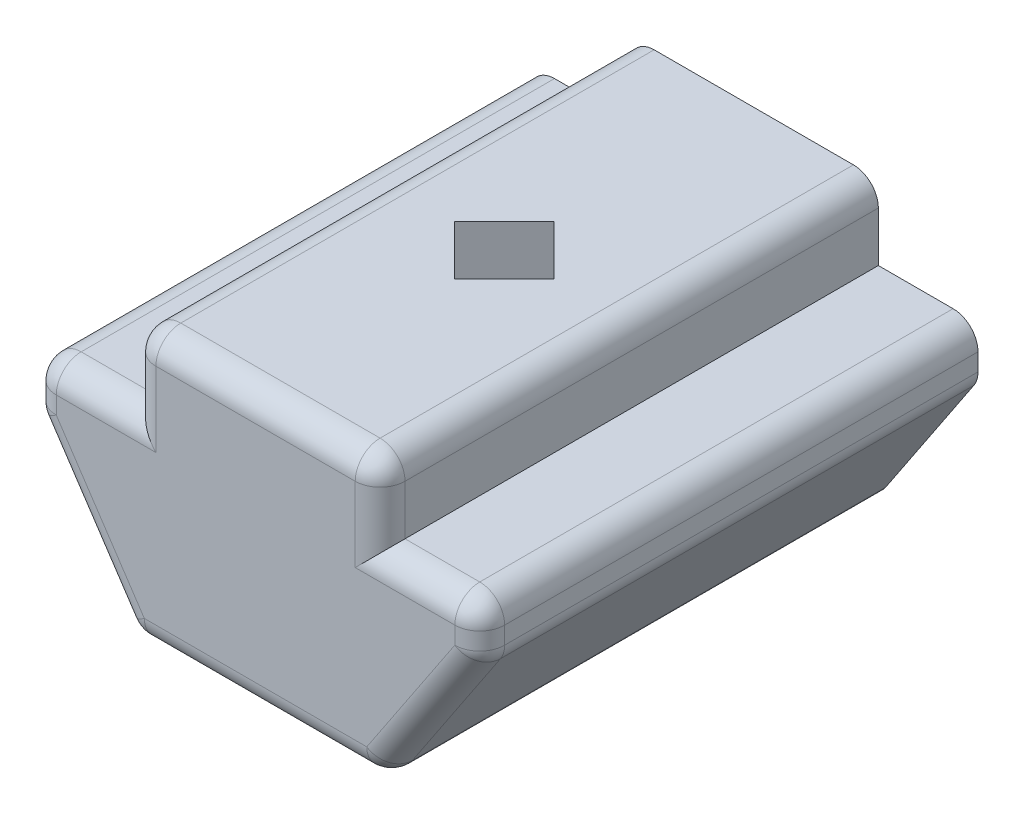
SolidWorks part; units mm, degrees
material "Maple"
ref_plane "Wasteboard" through (0, 0, 0) normal (0, 0, 1) x (1, 0, 0)
ref_plane "Left-Right" through (0, 0, 0) normal (0, 1, 0) x (1, 0, 0)
ref_plane "Front-Back" through (0, 0, 0) normal (1, 0, 0) x (0, 0, -1)
sketch "Sketch1" plane through (0, 0, 0) normal (0, 0, 1) x (1, 0, 0)
  line L10 (-2.5, -4.0476) -> (2.5, -4.0476)
  line L11 (2.5, -4.0476) -> (4.5, -1.0476)
  line L12 (4.5, -1.0476) -> (4.5, -0.0476)
  line L13 (4.5, -0.0476) -> (2.5, -0.0476)
  line L14 (2.5, -0.0476) -> (2.5, 1.4524)
  line L15 (2.5, 1.4524) -> (-2.5, 1.4524)
  line L16 (0, 1.4524) -> (0, 9.7381) construction
  line L17 (-2.5, -0.0476) -> (-2.5, 1.4524)
  line L18 (-4.5, -0.0476) -> (-2.5, -0.0476)
  line L19 (-4.5, -1.0476) -> (-4.5, -0.0476)
  line L20 (-2.5, -4.0476) -> (-4.5, -1.0476)
  point P14 (0, -4.0476)
  dimension "D1" = 5
  dimension "D2" = 5
  dimension "D3" = 3
  dimension "D4" = 1
  dimension "D5" = 1.5
  dimension "D6" = 2
extrude "Boss-Extrude1" add sketch "Sketch1" along normal blind 10
sketch "Sketch4" plane through (0, 1.4524, 0) normal (0, 1, 0) x (1, 0, 0)
  line L1 (-1.0211, -4.9865) -> (-0.0211, -3.9865)
  line L2 (-1.0211, -4.9865) -> (-0.0211, -5.9865)
  line L3 (-0.0211, -5.9865) -> (0.9789, -4.9865)
  line L4 (2.5, 0) -> (-2.5, 0)
  line L5 (-2.5, 0) -> (-2.5, -10)
  line L6 (-2.5, -10) -> (2.5, -10)
  line L7 (2.5, -10) -> (2.5, 0)
  line L8 (2.5, 0) -> (-2.5, 0) construction
  line L9 (-2.5, 0) -> (-2.5, -10) construction
  line L10 (-2.5, -10) -> (2.5, -10) construction
  line L11 (2.5, -10) -> (2.5, 0) construction
  line L12 (-0.0211, -3.9865) -> (0.9789, -4.9865)
  line L13 (-0.7282, -4.2794) -> (0.686, -5.6936) construction
  line L14 (-0.7282, -5.6936) -> (0.686, -4.2794) construction
  circle A0 centre (-0.0211, -4.9865) radius 1 construction
  dimension "D2" = 2
  dimension "D1" = 0
extrude "Cut-Extrude2" cut sketch "Sketch4" against normal through all
fillet "Fillet1" radius 0.5 8 edges at (2.5, -4.0476, 5) (-2.5, -4.0476, 5) (4.5, -1.0476, 5) (4.5, -0.0476, 5) (2.5, 1.4524, 5) (-4.5, -1.0476, 5) (-4.5, -0.0476, 5) (-2.5, 1.4524, 5)
fillet "Fillet2" radius 0.5 18 edges at (3.25, -0.0476, 10) (4.3536, -0.1941, 10) (4.5, -0.7219, 10) (4.4785, -1.0411, 10) (3.5322, -2.4993, 10) (2.4683, -3.9885, 10) (0, -4.0476, 10) (-2.4683, -3.9885, 10) (-3.5322, -2.4993, 10) (-4.4785, -1.0411, 10) (-4.5, -0.7219, 10) (-4.3536, -0.1941, 10) (2.5, 0.4524, 10) (2.3536, 1.3059, 10) (-2.5, 0.4524, 10) (-2.3536, 1.3059, 10) (-3.25, -0.0476, 10) (0, 1.4524, 10)
